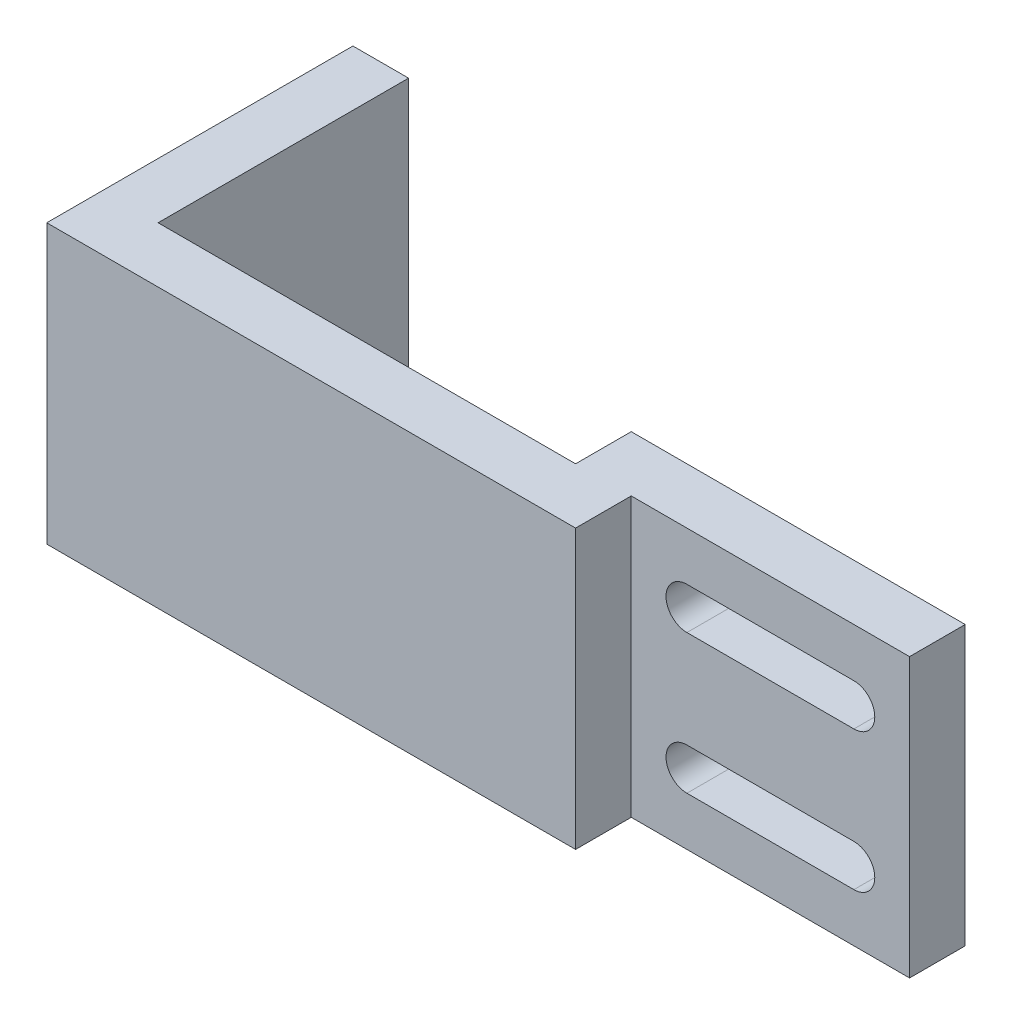
SolidWorks part; units mm, degrees
ref_plane "Front Plane" through (0, 0, 0) normal (0, 0, 1) x (1, 0, 0)
ref_plane "Top Plane" through (0, 0, 0) normal (0, 1, 0) x (1, 0, 0)
ref_plane "Right Plane" through (0, 0, 0) normal (1, 0, 0) x (0, 0, -1)
sketch "Croquis1" plane through (0, 0, 0) normal (0, 1, 0) x (1, 0, 0)
  line L0 (-19, 22) -> (-15, 22)
  line L1 (-15, 22) -> (-15, 4)
  line L2 (-15, 4) -> (15, 4)
  line L3 (15, 4) -> (15, 8)
  line L4 (15, 8) -> (39, 8)
  line L5 (39, 8) -> (39, 4)
  line L6 (39, 4) -> (19, 4)
  line L7 (19, 4) -> (19, 0)
  line L8 (19, 0) -> (-19, 0)
  line L9 (-19, 0) -> (-19, 22)
  point P2 (0, 0)
  dimension "D1" = 38
  dimension "D2" = 4
  dimension "D3" = 4
  dimension "D4" = 4
  dimension "D5" = 22
  dimension "D6" = 8
  dimension "D7" = 4
  dimension "D8" = 24
extrude "Saliente-Extruir1" add sketch "Croquis1" along normal blind 20
sketch "Croquis2" plane through (0, 0, -4) normal (0, 0, 1) x (1, 0, 0)
  line L0 (39, 10) -> (19, 10) construction
  line L1 (39, 20) -> (39, 0) construction
  line L2 (29, 20) -> (29, 10) construction
  line L3 (19, 20) -> (39, 20) construction
  line L4 (29, 15) -> (39, 15) construction
  line L5 (19, 20) -> (19, 0) construction
  line L6 (35, 16.5) -> (23, 16.5)
  line L7 (35, 13.5) -> (23, 13.5)
  line L8 (35, 3.5) -> (23, 3.5)
  line L9 (35, 6.5) -> (23, 6.5)
  arc A0 (35, 13.5) -> (35, 16.5) centre (35, 15) ccw
  arc A1 (23, 13.5) -> (23, 16.5) centre (23, 15) cw
  arc A2 (35, 6.5) -> (35, 3.5) centre (35, 5) cw
  arc A3 (23, 6.5) -> (23, 3.5) centre (23, 5) ccw
  point P15 (29, 13.5)
  point P20 (29, 16.5)
  dimension "D1" = 3
  dimension "D2" = 6
extrude "Cortar-Extruir1" cut sketch "Croquis2" against normal blind 20
